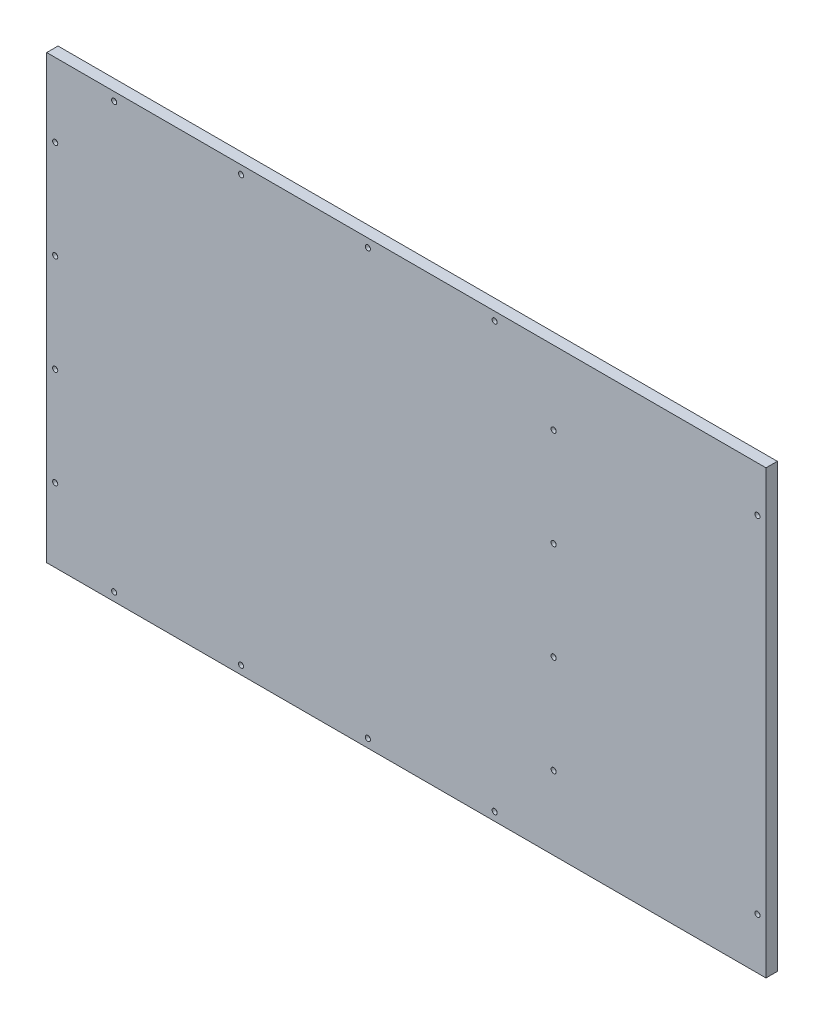
SolidWorks part; units mm, degrees
material "Maple"
ref_plane "Front Plane" through (0, 0, 0) normal (0, 0, 1) x (1, 0, 0)
ref_plane "Top Plane" through (0, 0, 0) normal (0, 1, 0) x (1, 0, 0)
ref_plane "Right Plane" through (0, 0, 0) normal (1, 0, 0) x (0, 0, -1)
sketch "Sketch1" plane through (0, 0, 0) normal (0, 0, 1) x (1, 0, 0)
  line L1 (403.3266, -247.7516) -> (-403.3266, -247.7516)
  line L2 (403.3266, -247.7516) -> (403.3266, 247.7516)
  line L3 (403.3266, 247.7516) -> (-403.3266, 247.7516)
  line L4 (-403.3266, -247.7516) -> (-403.3266, 247.7516)
  line L5 (403.3266, -247.7516) -> (-403.3266, 247.7516) construction
  line L6 (403.3266, 247.7516) -> (-403.3266, -247.7516) construction
  point P0 (0, 0)
  dimension "D1" = 495.5032
  dimension "D2" = 806.6532
extrude "Boss-Extrude1" add sketch "Sketch1" along normal blind 12.7
sketch "Sketch2" plane through (0, 0, 12.7) normal (0, 0, 1) x (1, 0, 0)
  line L0 (-403.3266, -228.7016) -> (-393.8016, -228.7016) construction
  line L1 (-403.3266, 247.7516) -> (-403.3266, -247.7516) construction
  line L2 (-393.8016, -165.3032) -> (-393.8016, -247.7516) construction
  line L3 (-403.3266, -247.7516) -> (403.3266, -247.7516) construction
  line L4 (-393.8016, -165.3032) -> (-374.7516, -165.3032) construction
  line L5 (-374.7516, -165.3032) -> (165.2016, -165.3032) construction
  circle A0 centre (-393.8016, -165.3032) radius 2.8956
  circle A1 centre (165.2016, -165.3032) radius 2.8956
  dimension "D4" = 5.7912
  dimension "D1" = 19.05
  dimension "D2" = 63.3984
  dimension "D3" = 9.525
  dimension "D5" = 19.05
  dimension "D6" = 539.9532
extrude "SideBarHoleMaster" cut sketch "Sketch2" against normal through all
sketch "Sketch3" plane through (0, 0, 0) normal (0, 0, -1) x (-1, 0, 0)
  circle A0 centre (-165.2016, -165.3032) radius 6.35
  circle A1 centre (393.8016, -165.3032) radius 6.35
  dimension "D1" = 12.7
extrude "Countersink" cut sketch "Sketch3" against normal offset from surface (8.89 mm away) 3.81 up to face at (168.0972, -165.3032, 12.7)
pattern_linear "LPattern1" count 4 spacing 110.2021 along (0, 1, 0) of "Countersink", "SideBarHoleMaster"
sketch "Sketch4" plane through (0, 0, 12.7) normal (0, 0, 1) x (1, 0, 0)
  line L0 (-403.3266, -238.2266) -> (-327.66, -238.2266) construction
  line L1 (-403.3266, 247.7516) -> (-403.3266, -247.7516) construction
  line L2 (-403.3266, -247.7516) -> (403.3266, -247.7516) construction
  line L3 (-403.3266, -238.2266) -> (-406.4, -238.2266) construction
  line L4 (403.3266, 247.7516) -> (-403.3266, 247.7516) construction
  circle A0 centre (-327.66, -238.2266) radius 2.8956
  circle A1 centre (-327.66, 238.2266) radius 2.8956
  point P9 (-327.66, 238.2266)
  dimension "D1" = 5.7912
  dimension "D2" = 9.525
  dimension "D3" = 3.0734
  dimension "D4" = 78.74
  dimension "D5" = 9.525
extrude "RearFrontBarMount" cut sketch "Sketch4" against normal through all
sketch "Sketch5" plane through (0, 0, 0) normal (0, 0, -1) x (-1, 0, 0)
  circle A0 centre (327.66, -238.2266) radius 6.35
  circle A1 centre (393.8016, -165.3032) radius 6.35 construction
  circle A2 centre (327.66, 238.2266) radius 6.35
extrude "RearFrontBarCounterSink" cut sketch "Sketch5" against normal offset from surface (8.89 mm away) 3.81 up to face at (-324.7644, 238.2266, 12.7)
pattern_linear "LPattern2" count 4 spacing 142.24 along (1, 0, 0) of "RearFrontBarMount", "RearFrontBarCounterSink"
sketch "Sketch6" plane through (0, 0, 12.7) normal (0, 0, 1) x (1, 0, 0)
  line L0 (393.8016, -247.7516) -> (393.8016, 196.7484) construction
  line L1 (-403.3266, -247.7516) -> (403.3266, -247.7516) construction
  line L2 (403.3266, -247.7516) -> (403.3266, 247.7516) construction
  circle A0 centre (393.8016, 196.7484) radius 2.8956
  circle A1 centre (393.8016, -190.6016) radius 2.8956
  dimension "D3" = 9.525
  dimension "D1" = 5.7912
  dimension "D2" = 444.5
  dimension "D4" = 57.15
extrude "EBForwardMountHole" cut sketch "Sketch6" against normal through all
sketch "Sketch7" plane through (0, 0, 0) normal (0, 0, -1) x (-1, 0, 0)
  circle A0 centre (-393.8016, 196.7484) radius 6.35
  circle A1 centre (-393.8016, -190.6016) radius 6.35
  dimension "D1" = 12.7
extrude "EB-Mounts-Countersinks" cut sketch "Sketch7" against normal offset from surface (8.89 mm away) 3.81 up to face at (396.6972, -190.6016, 12.7)
equation "\"Height\"= 32in"
equation "\"Width\"= 23in"
equation "\"Depth\"= 20in"
equation "\"Plexi\"= .121in"
equation "\"MagnetThickness\"= 0.125in"
equation "\"MagnetDiameter\"= 12mm"
equation "\"DoorPlexi\" = \"Plexi\""
equation "\"BasePlateThickness\" = 0.5in"
equation "\"BasePlateWidth\" = \"Width\"+\"EBWidth\"-2*\"Plexi\""
equation "\"Boxsize\" = .75in"
equation "\"Boxinner\" = .625in"
equation "\"CornerCube\" = 0.75in"
equation "\"FingerLength\" = 1.125in"
equation "\"Cutwidth\"= .016in"
equation "\"Earsize\"= 1in + \"Cutwidth\" /2"
equation "\"Slotsize\" = 1in - \"CutWidth\" / 2"
equation "\"InnerWidth\" = \"Width\" - 2* \"Plexi\""
equation "\"InnerHeight\" = \"Height\" -2 * \"Plexi\""
equation "\"InnerDepth\" = \"Depth\" - 2*\"Plexi\""
equation "\"RearNumHoles\" = 4"
equation "\"RearHolesBorder\" = 2.25"
equation "\"RearHoleSpacing\" = (\"Width\" - 2*\"RearHolesBorder\") / (\"RearNumHoles\"-1)"
equation "\"RearBarLength\" = (\"InnerWidth\"-2*\"CornerCube\")"
equation "\"RearTopNumHoles\" = 4"
equation "\"RearTopHolesBorder\" = 3.1"
equation "\"RearTopHolesSpacing\" = (\"Width\" - 2*\"RearTopHolesBorder\") / (\"RearTopNumHoles\"-1)"
equation "\"SideTopNumHoles\" = 4"
equation "\"SideTopHoleOffset\"=\"CornerCube\"+\"FingerLength\"+\"Plexi\"+.5"
equation "\"SideTopHoleSpacing\" = (\"TopBarDepth\"-2*\"SideTopHoleOffset\") / (\"SideTopNumHoles\"-1)"
equation "\"SideHorizNumHoles\" = 4"
equation "\"SideHorizHoleBorder\" = 1.50"
equation "\"SideHorizHoleSpacing\" = (\"TopBarDepth\"-2*\"SideHorizHoleBorder\") / (\"SideHorizNumHoles\"-1)"
equation "\"SideVertBarLength\"=\"Height\"-\"BasePlateThickness\"-2*\"CornerCube\"-\"Plexi\""
equation "\"SideVertNumHoles\" = 4"
equation "\"SideVertHolesBorder\" = \"CornerCube\"+\"FingerLength\"+1.50"
equation "\"SideVertHoleSpacing\" = (\"SideVertBarLength\" - 2*(\"SideVertHolesBorder\"-\"Plexi\"-\"CornerCube\")) / (\"SideVertNumHoles\"-1)"
equation "\"RearSideVertNumHoles\" = 4"
equation "\"RearSideVertHolesBorder\" = 2.4"
equation "\"RearSideVertHoleSpacing\" = (\"SideVertBarLength\" - 2*(\"RearSideVertHolesBorder\"-\"Plexi\"-\"CornerCube\")) / (\"RearSideVertNumHoles\"-1)"
equation "\"RivetDia\" = .228in"
equation "\"SlotDepth\" = \"Plexi\" + 0.75in + .005in"
equation "\"SideSlotWidth\"   = \"Plexi\"+.005in"
equation "\"SidePanelVertSpacing\" = (\"Height\"-2*(1.75-\"Plexi\")) / 5"
equation "\"BottomPanelSideHoleSpacing\" = (\"InnerDepth\"-2*(1.75-\"Plexi\")) / 4"
equation "\"FrontDoorGap\" = .1in"
equation "\"TopDepth\" = \"Depth\"-\"DoorPlexi\"-\"FrontDoorGap\""
equation "\"TopBarDepth\" = \"Depth\"-\"DoorPlexi\"-\"Plexi\"-2*\"MagnetThickness\"-2*\"CornerCube\""
equation "\"BasePlateDepth\" = \"TopBarDepth\"+2*\"CornerCube\""
equation "\"D1@Sketch1\"=\"BasePlateDepth\""
equation "\"D2@Sketch1\"=\"BasePlateWidth\""
equation "\"D1@Boss-Extrude1\"=\"BasePlateThickness\""
equation "\"EBWidth\" = 9in"
equation "\"BoxsizeHalf\" = \"Boxsize\"/2"
equation "\"FingerWidth\" = .625in"
equation "\"CoolerDepth\" = 12in"
equation "\"ShelfGap\" = 0.5in"
equation "\"ShelfDepth\" = \"TopBarDepth\"+\"CornerCube\"-\"CoolerDepth\""
equation "\"ShelfBarDepth\"=\"ShelfDepth\"-2*\"CornerCube\""
equation "\"ShelfWidth\" = \"EBWidth\"-\"ShelfGap\""
equation "\"ShelfBarWidth\" = \"EBWidth\"-\"Boxsize\""
equation "\"ShelfBarWidthShort\" = \"ShelfBarWidth\"-\"Boxsize\"-\"ShelfGap\""
equation "\"IntakeWidth\"=4in"
equation "\"IntakeHeight\"=2in"
equation "\"ExhaustWidth\"=4in"
equation "\"ExhaustHeight\"=2in"
equation "\"VentSpacing\"=7in"
equation "\"AngleBracketLength\"=20mm"
equation "\"AngleBracketWidth\"=.5in"
equation "\"AngleBracketThickness\"=.125in"
equation "\"AngleBracketHolePos\"=15mm"
equation "\"AngleBracketHoleDia\"=\"Rivet3_16Dia\""
equation "\"ShelfBarAngleHole\"=\"ShelfGap\"+\"Boxsize\"+\"AngleBracketHolePosShort\""
equation "\"D1@Sketch2\"=\"Boxsize\""
equation "\"D2@Sketch2\"=\"SideTopHoleOffset\""
equation "\"D3@Sketch2\"=\"BoxsizeHalf\""
equation "\"ComponentMountDia\"=0.1770"
equation "\"ShelfThickness\" = .1250in"
equation "\"BinderPostDia\" = .228in"
equation "\"ShelfHeight1\" = 13in"
equation "\"ShelfHeight2\" = 24in"
equation "\"VentVertLocation\"=12.75in"
equation "\"PSBracketThickness\" = .0641in"
equation "\"D4@Sketch2\"=\"BinderPostDia\""
equation "\"D5@Sketch2\"=\"Boxsize\""
equation "\"D6@Sketch2\"=\"RearBarLength\""
equation "\"D1@LPattern1\"=\"SideTopNumHoles\""
equation "\"D3@LPattern1\"=\"SideTopHoleSpacing\""
equation "\"D1@Sketch4\"=\"BinderPostDia\""
equation "\"D2@Sketch4\"=\"BoxsizeHalf\""
equation "\"D3@Sketch4\"=\"Plexi\""
equation "\"D4@Sketch4\"=\"RearTopHolesBorder\""
equation "\"D3@LPattern2\"=\"RearTopHolesSpacing\""
equation "\"D1@LPattern2\"=\"RearTopNumHoles\""
equation "\"D1@Sketch6\"=\"BinderPostDia\""
equation "\"EBForwardMountOffset\" = 4.0in"
equation "\"EBForwardMount\" = 2*\"Boxsize\"+\"CoolerDepth\"+\"EBForwardMountOffset\""
equation "\"D2@Sketch6\"=\"EBForwardMount\""
equation "\"D3@Sketch6\"=\"BoxsizeHalf\""
equation "\"EBRearwardMountOffset\" = 1.5in"
equation "\"EBRearwardMount\"= \"Boxsize\"+\"EBRearwardMountOffset\""
equation "\"D4@Sketch6\"=\"EBRearwardMount\""
equation "\"D5@Sketch4\"=\"BoxsizeHalf\""
